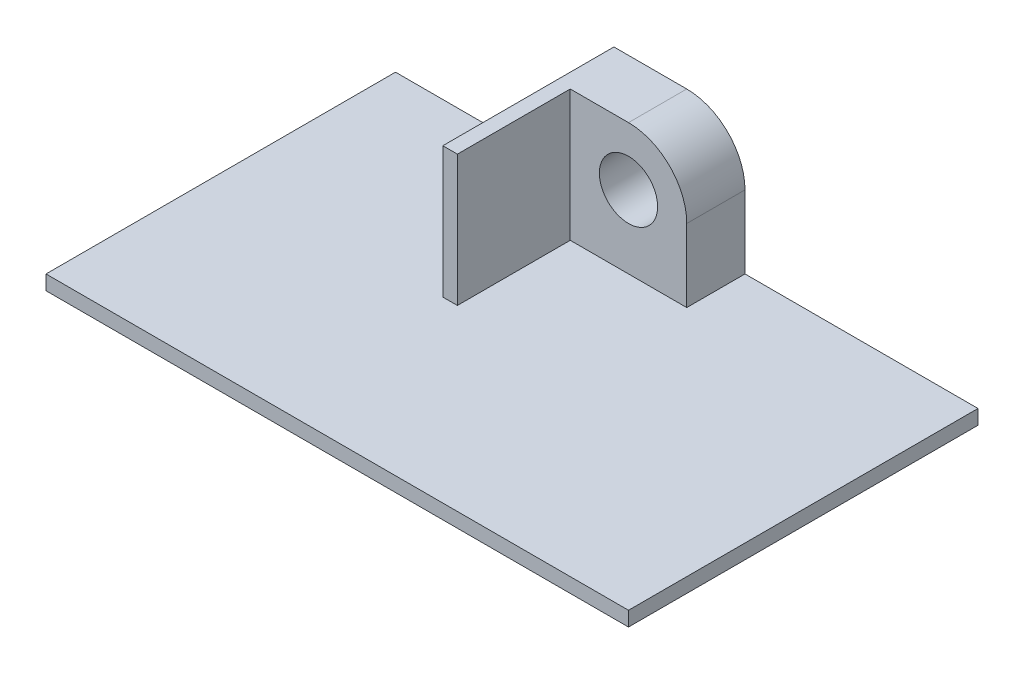
SolidWorks part; units mm, degrees
ref_plane "Front Plane" through (0, 0, 0) normal (0, 0, 1) x (1, 0, 0)
ref_plane "Top Plane" through (0, 0, 0) normal (0, 1, 0) x (1, 0, 0)
ref_plane "Right Plane" through (0, 0, 0) normal (1, 0, 0) x (0, 0, -1)
sketch "Sketch1" plane through (0, 0, 0) normal (0, 0, 1) x (1, 0, 0)
  line L1 (0, 0) -> (63.5, 0)
  line L2 (0, 0) -> (0, 1.5875)
  line L3 (0, 1.5875) -> (63.5, 1.5875)
  line L4 (63.5, 0) -> (63.5, 1.5875)
  dimension "D1" = 1.5875
  dimension "D2" = 63.5
extrude "Boss-Extrude1" add sketch "Sketch1" along normal blind 38.1
sketch "Sketch2" plane through (0, 0, 0) normal (0, 0, -1) x (-1, 0, 0)
  line L0 (0, 0) -> (-63.5, 0) construction
  line L1 (-63.5, 0) -> (-63.5, 1.5875) construction
  line L2 (-38.1, 9.525) -> (-38.1, 1.5875)
  line L3 (-63.5, 1.5875) -> (0, 1.5875) construction
  line L4 (-38.1, 1.5875) -> (-25.4, 1.5875)
  line L5 (-25.4, 1.5875) -> (-25.4, 9.525)
  line L6 (-31.75, 15.875) -> (-25.4, 15.875)
  line L7 (-25.4, 15.875) -> (-25.4, 9.525)
  circle A0 centre (-31.75, 9.525) radius 3.175
  arc A1 (-31.75, 15.875) -> (-38.1, 9.525) centre (-31.75, 9.525) ccw
  dimension "D1" = 6.35
  dimension "D4" = 12.7
  dimension "D2" = 9.525
  dimension "D3" = 31.75
extrude "Boss-Extrude2" add sketch "Sketch2" against normal blind 6.35
sketch "Sketch3" plane through (0, 1.5875, 0) normal (0, 1, 0) x (1, 0, 0)
  line L1 (25.4, 0) -> (23.8125, 0)
  line L2 (25.4, 0) -> (25.4, -18.6531)
  line L3 (25.4, -18.6531) -> (23.8125, -18.6531)
  line L4 (23.8125, 0) -> (23.8125, -18.6531)
  dimension "D1" = 1.5875
  dimension "D2" = 18.6531
extrude "Boss-Extrude3" add sketch "Sketch3" along normal up to surface (14.2875 mm away) up to face at (28.575, 15.875, 3.175)
